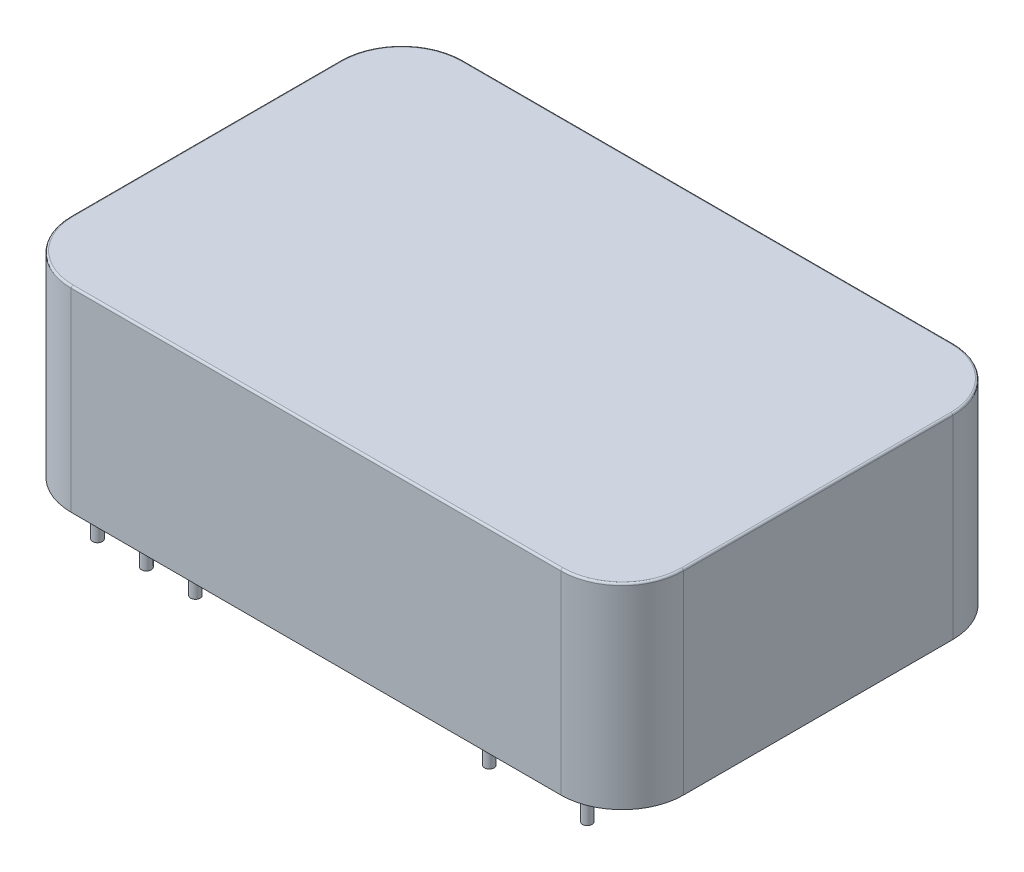
SolidWorks part; units mm, degrees
ref_plane "Front Plane" through (0, 0, 0) normal (0, 0, 1) x (1, 0, 0)
ref_plane "Top Plane" through (0, 0, 0) normal (0, 1, 0) x (1, 0, 0)
ref_plane "Right Plane" through (0, 0, 0) normal (1, 0, 0) x (0, 0, -1)
sketch "Sketch1" plane through (0, 0, 0) normal (0, 1, 0) x (1, 0, 0)
  line L1 (15.875, 10.16) -> (-15.875, 10.16)
  line L2 (15.875, 10.16) -> (15.875, -10.16)
  line L3 (15.875, -10.16) -> (-15.875, -10.16)
  line L4 (-15.875, 10.16) -> (-15.875, -10.16)
  line L5 (15.875, 10.16) -> (-15.875, -10.16) construction
  line L6 (15.875, -10.16) -> (-15.875, 10.16) construction
  point P0 (0, 0)
  dimension "D1" = 31.75
  dimension "D2" = 20.32
extrude "Boss-Extrude1" add sketch "Sketch1" along normal blind 10.16
sketch "Sketch2" plane through (0, 0, 0) normal (0, -1, 0) x (1, 0, 0)
  line L0 (-15.875, -10.16) -> (-15.875, 10.16) construction
  circle A0 centre (-13.875, 7.62) radius 0.25
  circle A1 centre (-11.335, 7.62) radius 0.25
  circle A2 centre (-8.795, 7.62) radius 0.25
  circle A3 centre (6.445, 7.62) radius 0.25
  circle A4 centre (11.525, 7.62) radius 0.25
  circle A5 centre (11.525, -7.62) radius 0.25
  circle A6 centre (6.445, -7.62) radius 0.25
  circle A7 centre (-8.795, -7.62) radius 0.25
  circle A8 centre (-11.335, -7.62) radius 0.25
  point P20 (0, 0)
  point P21 (0, 0)
  point P22 (0, 0)
  point P23 (0, 0)
  point P25 (0, 0)
  point P26 (0, 0)
  point P27 (0, 0)
  dimension "D8" = 0.5
  dimension "D1" = 2
  dimension "D2" = 2.54
  dimension "D3" = 2.54
  dimension "D4" = 22.86
  dimension "D5" = 5.08
  dimension "D6" = 15.24
  dimension "D7" = 7.62
extrude "Boss-Extrude2" add sketch "Sketch2" along normal blind 3.05
fillet "Fillet1" radius 3.18 4 edges at (15.875, 5.08, -10.16) (15.875, 5.08, 10.16) (-15.875, 5.08, -10.16) (-15.875, 5.08, 10.16)
fillet "Fillet2" radius 0.1 8 edges at (14.9436, 10.16, 9.2286) (0, 10.16, 10.16) (-14.9436, 10.16, 9.2286) (-15.875, 10.16, 0) (-14.9436, 10.16, -9.2286) (0, 10.16, -10.16) (14.9436, 10.16, -9.2286) (15.875, 10.16, 0)
